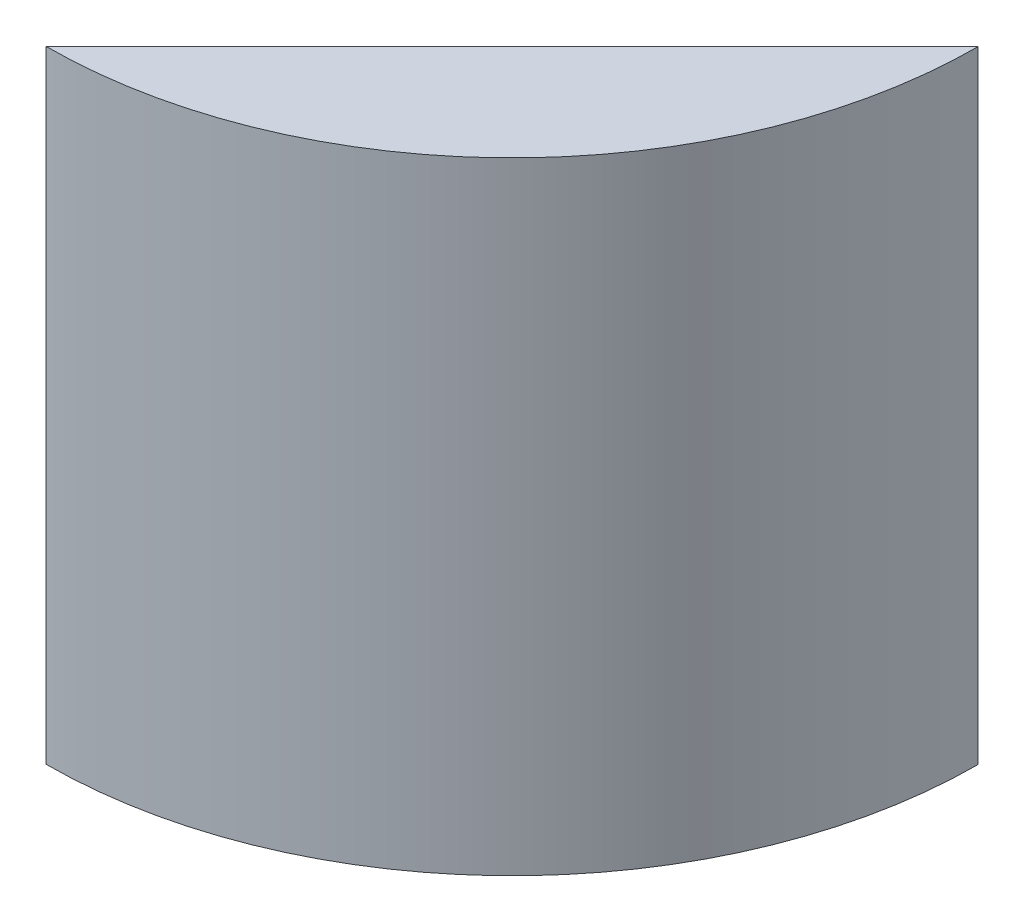
SolidWorks part; units mm, degrees
ref_plane "Front Plane" through (0, 0, 0) normal (0, 0, 1) x (1, 0, 0)
ref_plane "Top Plane" through (0, 0, 0) normal (0, 1, 0) x (1, 0, 0)
ref_plane "Right Plane" through (0, 0, 0) normal (1, 0, 0) x (0, 0, -1)
sketch "Sketch1" plane through (0, 0, 0) normal (0, 1, 0) x (1, 0, 0)
  circle A0 centre (0, 0) radius 85.725
extrude "Boss-Extrude1" add sketch "Sketch1" along normal blind 114.3
sketch "Sketch2" plane through (0, 114.3, 0) normal (0, 1, 0) x (1, 0, 0)
  line L0 (85.7249, -0.1067) -> (0, -85.725)
  line L1 (0, -85.725) -> (-45.6275, -96.7194)
  line L6 (-45.6275, -96.7194) -> (-137.4289, 46.1739)
  line L7 (-137.4289, 46.1739) -> (19.1253, 101.9105)
  line L8 (19.1253, 101.9105) -> (109.8339, 30.6005)
  line L9 (109.8339, 30.6005) -> (85.7249, -0.1067)
  circle A0 centre (0, 0) radius 85.725 construction
extrude "Cut-Extrude1" cut sketch "Sketch2" against normal blind 152.4
sketch "Sketch3" plane through (42.8625, 0, 42.9158) normal (-0.7067, 0, -0.7075) x (-0.7075, 0, 0.7067)
  line L0 (60.579, 0) -> (-60.579, 0) construction
  line L1 (-60.579, 0) -> (-60.579, 114.3) construction
  circle A0 centre (-37.719, 87.122) radius 2.7781
  circle A1 centre (-14.859, 87.122) radius 2.7781
  circle A2 centre (-37.719, 29.21) radius 2.7781
  circle A3 centre (-14.859, 29.21) radius 2.7781
  circle A4 centre (6.6437, 73.636) radius 2.7781
  circle A5 centre (26.9637, 73.636) radius 2.7781
  dimension "D1" = 29.21
  dimension "D7" = 20.32
  dimension "D2" = 57.912
  dimension "D3" = 22.86
  dimension "D4" = 22.86
  dimension "D5" = 57.912
  dimension "D6" = 22.86
extrude "Cut-Extrude2" cut sketch "Sketch3" against normal blind 12.7
sketch "Sketch4" plane through (0, 0, 0) normal (0, -1, 0) x (-1, 0, 0)
  line L0 (-42.8625, -42.9158) -> (-60.579, -60.6544) construction
  line L1 (0, -85.725) -> (-85.7249, -0.1067) construction
  arc A0 (-85.7249, -0.1067) -> (0, -85.725) centre (0, 0) ccw construction
  circle A1 centre (-51.7207, -51.7851) radius 6.985
  dimension "D1" = 13.97
extrude "Cut-Extrude3" cut sketch "Sketch4" against normal blind 6.096
